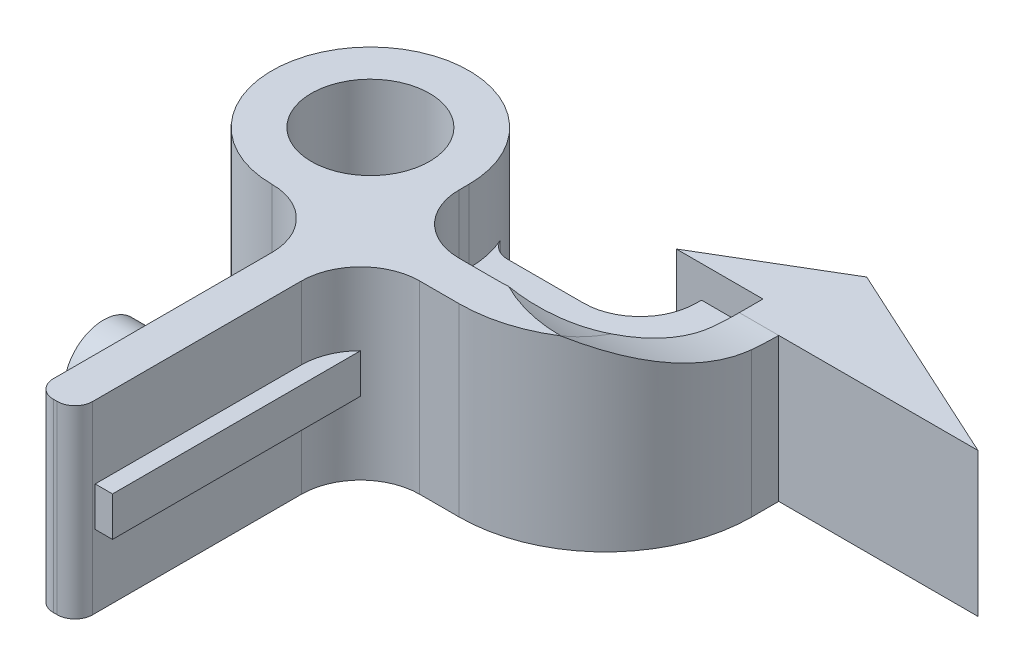
SolidWorks part; units mm, degrees
ref_plane "Front Plane" through (0, 0, 0) normal (0, 0, 1) x (1, 0, 0)
ref_plane "Top Plane" through (0, 0, 0) normal (0, 1, 0) x (1, 0, 0)
ref_plane "Right Plane" through (0, 0, 0) normal (1, 0, 0) x (0, 0, -1)
sketch "Sketch1" plane through (0, 0, 0) normal (0, 1, 0) x (1, 0, 0)
  line L0 (3, -8) -> (3, -19.1)
  line L1 (3.9, -20) -> (4.1, -20)
  line L2 (5, -19.1) -> (5, -8.5)
  line L6 (0, -3) -> (0, -5)
  line L7 (3, 0) -> (3, -4) construction
  line L8 (8, -5.5) -> (10, -5.5)
  line L9 (27.5479, 3.3) -> (17.43, 3.3)
  line L10 (17.43, 3.3) -> (17.43, 1.93)
  line L11 (27.5479, 3.3) -> (17.0975, 8.1)
  line L12 (17.0975, 8.1) -> (11.03, 4.5)
  line L13 (11.03, 4.5) -> (15.43, 4.5)
  line L14 (15.43, 1.93) -> (15.43, 4.5)
  line L15 (8, -3.5) -> (10, -3.5)
  line L16 (5, -0.5) -> (5, 0)
  circle A0 centre (0, 0) radius 3
  arc A1 (5, 0) -> (0, -5) centre (0, 0) ccw
  arc A2 (3, -4) -> (5, 0) centre (0, 0) ccw construction
  arc A3 (3, -8) -> (0, -5) centre (0, -8) ccw
  arc A4 (5, -8.5) -> (8, -5.5) centre (8, -8.5) cw
  arc A5 (10, -5.5) -> (17.43, 1.93) centre (10, 1.93) ccw
  arc A6 (10, -3.5) -> (15.43, 1.93) centre (10, 1.93) ccw
  arc A7 (8, -3.5) -> (5, -0.5) centre (8, -0.5) cw
  arc A8 (5, -19.1) -> (4.1, -20) centre (4.1, -19.1) cw
  arc A9 (3.9, -20) -> (3, -19.1) centre (3.9, -19.1) cw
  point P9 (8, -8.5)
  point P11 (5, -8.5)
  point P28 (8, -0.5)
  point P29 (8, -3.5)
  point P33 (5, -20)
  point P37 (9, -5.5)
  dimension "D1" = 10
  dimension "D2" = 6
  dimension "D4" = 20
  dimension "D5" = 11.5
  dimension "D3" = 3
  dimension "D12" = 7.0551
  dimension "D7" = 7.43
  dimension "D17" = 0.9
  dimension "D6" = 3
  dimension "D8" = 2
  dimension "D9" = 3
  dimension "D10" = 5
  dimension "D11" = 8.8
  dimension "D13" = 4.4
  dimension "D14" = 13.6
  dimension "D15" = 10
  dimension "D16" = 11.5
extrude "Boss-Extrude1" add sketch "Sketch1" along normal blind 9.38 contours A0 | L0 A9 L1 A8 L2 A4 L8 A5 L10 L9 L11 L12 L13 L14 A6 L15 A7 L16 A1 A3
ref_plane "Plane1" through (0, 4.69, 0) normal (0, 1, 0) x (1, 0, 0)
sketch "Sketch3" plane through (0, 4.69, 0) normal (0, 1, 0) x (1, 0, 0)
  line L0 (11.03, 4.5) -> (15.43, 4.5) construction
  line L1 (9.4436, 1.3758) -> (5.6017, 1.3758)
  line L2 (5, 0) -> (5, -0.5)
  line L3 (8, -3.5) -> (10, -3.5) construction
  line L4 (8, -3.5) -> (10, -3.5)
  line L5 (15.43, 1.93) -> (15.43, 4.5) construction
  line L6 (15.43, 1.93) -> (15.43, 4.5)
  line L7 (15.43, 4.5) -> (12.3099, 4.5)
  line L8 (12.3099, 4.242) -> (12.3099, 4.5)
  arc A1 (5.6017, 1.3758) -> (4.5608, 2.0493) centre (5.6017, 2.517) cw
  arc A2 (5, 0) -> (0, -5) centre (0, 0) ccw construction
  arc A3 (4.5608, 2.0493) -> (5, 0) centre (0, 0) cw
  arc A4 (5, -0.5) -> (8, -3.5) centre (8, -0.5) ccw
  arc A5 (10, -3.5) -> (15.43, 1.93) centre (10, 1.93) ccw
  arc A6 (9.4436, 1.3758) -> (12.3099, 4.242) centre (9.4436, 4.242) ccw
  point P0 (12.3099, 4.5)
  dimension "D1" = 2.8662
  dimension "D3" = 1.1411
  dimension "D2" = 0.258
  dimension "D4" = 3.1201
extrude "Boss-Extrude2" add sketch "Sketch3" along normal mid plane 2
sketch "Sketch5" plane through (3, 0, 0) normal (-1, 0, 0) x (0, 0, 1)
  line L0 (12.55, 9.38) -> (12.55, 0) construction
  line L1 (20, 9.38) -> (20, 0) construction
  line L2 (8, 9.38) -> (19.1, 9.38) construction
  line L3 (8, 0) -> (19.1, 0) construction
  circle A0 centre (12.55, 4.69) radius 2
  dimension "D2" = 4
  dimension "D1" = 7.45
extrude "Boss-Extrude3" add sketch "Sketch5" along normal blind 4
sketch "Sketch6" plane through (0, 4.69, 0) normal (0, 1, 0) x (1, 0, 0)
  line L0 (5.8787, -6.3787) -> (5.8787, -18.9728)
  line L1 (5.8787, -18.9728) -> (5, -18.9728)
  line L2 (5, -18.9728) -> (5, -8.5)
  arc A0 (8, -5.5) -> (5, -8.5) centre (8, -8.5) ccw construction
  arc A1 (5, -8.5) -> (5.8787, -6.3787) centre (8, -8.5) cw
  dimension "D1" = 12.5942
extrude "Boss-Extrude4" add sketch "Sketch6" along normal mid plane 2 contours A1 L2 L1 L0
ref_plane "Plane2" through (14, 0, 0) normal (1, 0, 0) x (0, 0, -1)
sketch "Sketch7" plane through (14, 0, 0) normal (1, 0, 0) x (0, 0, -1)
  line L0 (1.93, 9.38) -> (-5.5, 9.38) construction
  line L1 (-4.3386, 9.38) -> (3.3, 22.3659)
  line L3 (3.3, 7.3) -> (8.1, 7.3)
  line L4 (8.1, 7.3) -> (8.1, 10.1958)
  line L5 (8.1, 10.1958) -> (3.3, 22.3659)
  arc A0 (-4.3386, 9.38) -> (3.3, 7.3) centre (3.3, 22.3659) ccw
  point P0 (-4.3386, 9.38)
  point P4 (3.3, 7.3)
  dimension "D1" = 2.08
  dimension "D2" = 4.8
  dimension "D3" = 4.8
  dimension "D4" = 13.0825
extrude "Cut-Extrude1" cut sketch "Sketch7" along normal blind 15
sketch "Sketch8" plane through (14, 0, 0) normal (1, 0, 0) x (0, 0, -1)
  line L0 (6.2622, 7.3) -> (4.5, 7.3)
  line L1 (4.5, 7.3) -> (4.5, 9.38)
  line L2 (4.5, 9.38) -> (6.2622, 9.38)
  line L3 (6.2622, 9.38) -> (6.2622, 7.3)
extrude "Cut-Extrude2" cut sketch "Sketch8" against normal blind 5
sketch "Sketch11" plane through (14, 0, 0) normal (1, 0, 0) x (0, 0, -1)
  line L0 (-4.3314, 9.3758) -> (3.3, 22.3659)
  line L1 (3.3, 22.3659) -> (3.3, 7.3)
  point P0 (-4.3314, 9.3758)
  point P1 (3.3, 7.3)
sketch "Sketch12" plane through (14, 0, 0) normal (1, 0, 0) x (0, 0, -1)
  line L0 (-1.7422, 9.38) -> (-1.7422, 8.1688)
  line L1 (-1.7422, 9.38) -> (-1.7422, 8.1688) construction
  line L3 (-4.3314, 9.3758) -> (-4.3314, 10.2132)
  line L4 (-4.3314, 10.2132) -> (-1.7422, 10.2132)
  line L5 (-1.7422, 10.2132) -> (-1.7422, 9.38)
  arc A0 (-4.3314, 9.3758) -> (1.93, 7.3624) centre (3.3, 22.3659) ccw construction
  arc A1 (-1.7422, 8.1688) -> (-4.3314, 9.3758) centre (3.3, 22.3659) cw
  arc A2 (-4.3314, 9.3758) -> (-1.7422, 8.1688) centre (3.3, 22.3659) ccw construction
  dimension "D1" = 2.5892
  dimension "D2" = 0.8374
revolve "Cut-Revolve2" cut sketch "Sketch12" angle 180 about L1
